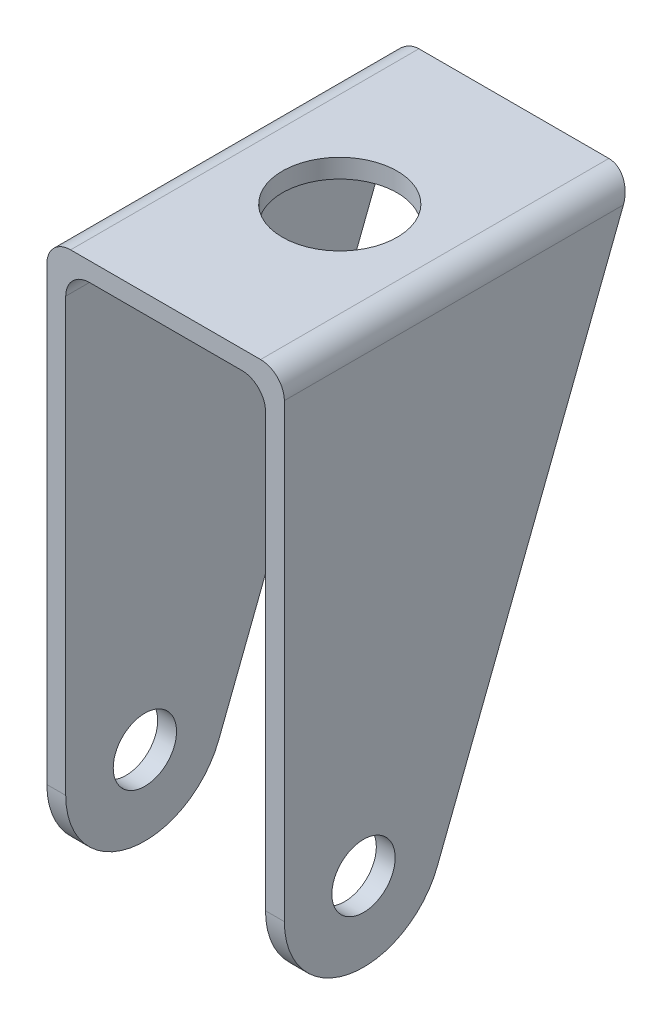
SolidWorks part; units mm, degrees
ref_plane "Alzado" through (0, 0, 0) normal (0, 0, 1) x (1, 0, 0)
ref_plane "Planta" through (0, 0, 0) normal (0, 1, 0) x (1, 0, 0)
ref_plane "Vista lateral" through (0, 0, 0) normal (1, 0, 0) x (0, 0, -1)
sketch "Croquis1" plane through (0, 0, 0) normal (0, 1, 0) x (1, 0, 0)
  line L1 (-15, -22) -> (15, -22)
  line L2 (-15, -22) -> (-15, 22)
  line L3 (-15, 22) -> (15, 22)
  line L4 (15, -22) -> (15, 22)
  line L5 (-15, -22) -> (15, 22) construction
  line L6 (-15, 22) -> (15, -22) construction
  circle A0 centre (0, 0) radius 7.25
  point P0 (0, 0)
  point P8 (0, 0)
  dimension "D3" = 14.5
  dimension "D1" = 30
  dimension "D2" = 44
extrude "Saliente-Extruir1" add sketch "Croquis1" against normal blind 2.38
sketch "Croquis2" plane through (15, 0, 0) normal (1, 0, 0) x (0, 0, -1)
  line L0 (-22, -60) -> (-22, 0)
  line L1 (-22, 0) -> (22, 0)
  line L4 (22, 0) -> (-2.6768, -63.6165)
  arc A0 (-22, -60) -> (-2.6768, -63.6165) centre (-12, -60) ccw
  circle A1 centre (-12, -60) radius 4
  dimension "D2" = 20
  dimension "D3" = 8
  dimension "D1" = 60
extrude "Saliente-Extruir2" add sketch "Croquis2" against normal blind 2.38
sketch "Croquis3" plane through (15, 0, 0) normal (1, 0, 0) x (0, 0, -1)
  line L0 (22, 0) -> (21.0768, -2.38)
  line L1 (21.0768, -2.38) -> (22, -2.38)
  line L2 (22, -2.38) -> (22, 0)
extrude "Cortar-Extruir1" cut sketch "Croquis3" against normal through all
sketch "Croquis4" plane through (-15, 0, 0) normal (-1, 0, 0) x (0, 0, 1)
  line L0 (-22, 0) -> (2.6768, -63.6165)
  line L1 (-22, 0) -> (-21.0768, -2.38) construction
  line L2 (-22, 0) -> (22, 0)
  line L3 (22, 0) -> (22, -60)
  arc A0 (2.6768, -63.6165) -> (22, -60) centre (12, -60) ccw
  arc A1 (2.6768, -63.6165) -> (22, -60) centre (12, -60) ccw construction
  circle A2 centre (12, -60) radius 4
  circle A3 centre (12, -60) radius 4 construction
extrude "Saliente-Extruir3" add sketch "Croquis4" against normal blind 2.38
fillet "Redondeo1" radius 3 1 edges at (12.62, -2.38, 0.4616)
fillet "Redondeo2" radius 3 1 edges at (-12.62, -2.38, 0.4616)
fillet "Redondeo3" radius 3 2 edges at (15, 0, 0) (-15, 0, 0)
